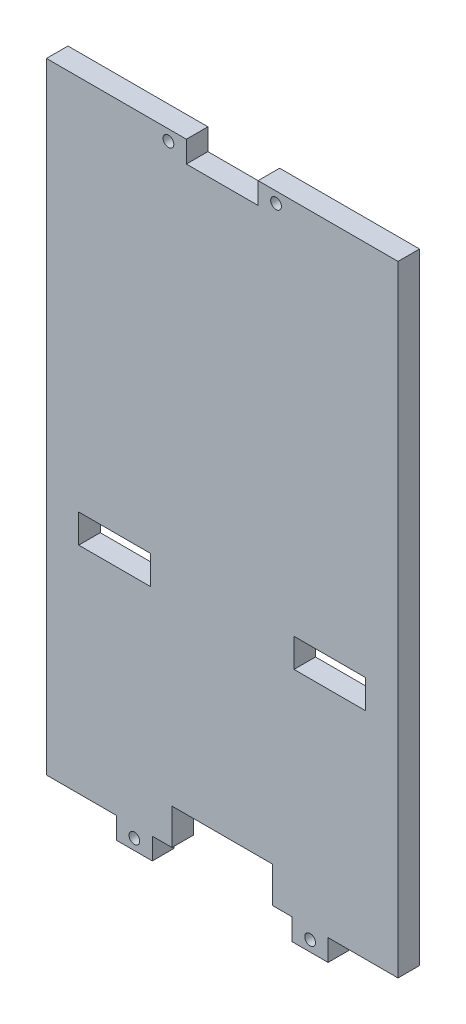
SolidWorks part; units mm, degrees
ref_plane "Plan de face" through (0, 0, 0) normal (0, 0, 1) x (1, 0, 0)
ref_plane "Plan de dessus" through (0, 0, 0) normal (0, 1, 0) x (1, 0, 0)
ref_plane "Plan de droite" through (0, 0, 0) normal (1, 0, 0) x (0, 0, -1)
sketch "Esquisse1" plane through (0, 0, 0) normal (0, 0, 1) x (1, 0, 0)
  line L0 (0, 176.8395) -> (0, -221.1538) construction
  line L1 (-49, 86.5) -> (49, 86.5)
  line L2 (-49, 86.5) -> (-49, -86.5)
  line L3 (-49, -86.5) -> (49, -86.5)
  line L4 (49, 86.5) -> (49, -86.5)
  line L5 (376.8436, 0) -> (-286.1998, 0) construction
  line L6 (-376.8436, 0) -> (286.1998, 0) construction
  line L7 (20, -18.5) -> (20, -26.5)
  line L8 (-40, -18.5) -> (-20, -18.5)
  line L9 (-40, -18.5) -> (-40, -26.5)
  line L10 (-40, -26.5) -> (-20, -26.5)
  line L11 (-20, -18.5) -> (-20, -26.5)
  line L12 (40, -26.5) -> (20, -26.5)
  line L13 (40, -18.5) -> (40, -26.5)
  line L14 (40, -18.5) -> (20, -18.5)
  dimension "D1" = 173
  dimension "D2" = 98
  dimension "D3" = 49
  dimension "D4" = 86.5
  dimension "D5" = 8
  dimension "D6" = 20
  dimension "D7" = 60
  dimension "D8" = 9
extrude "Boss.-Extru.1" add sketch "Esquisse1" along normal blind 6
sketch "Esquisse2" plane through (0, 0, 6) normal (0, 0, 1) x (1, 0, 0)
  line L1 (-49, -86.5) -> (49, -86.5) construction
  line L2 (29.5, -86.5) -> (19.5, -86.5)
  line L3 (29.5, -86.5) -> (29.5, -92.5)
  line L4 (29.5, -92.5) -> (19.5, -92.5)
  line L6 (154.6429, 0) -> (-167.6281, 0) construction
  line L7 (19.5, -86.5) -> (19.5, -92.5)
  line L8 (-49, 86.5) -> (-49, -86.5) construction
  line L9 (-19.5, -86.5) -> (-29.5, -86.5)
  line L10 (-19.5, -86.5) -> (-19.5, -92.5)
  line L11 (-19.5, -92.5) -> (-29.5, -92.5)
  line L12 (-29.5, -86.5) -> (-29.5, -92.5)
  dimension "D1" = 6
  dimension "D2" = 6
  dimension "D3" = 10
  dimension "D4" = 10
  dimension "D5" = 19.5
  dimension "D6" = 39
extrude "Boss.-Extru.2" add sketch "Esquisse2" against normal blind 6
sketch "Esquisse3" plane through (0, 0, 6) normal (0, 0, 1) x (1, 0, 0)
  line L0 (-49, 86.5) -> (-49, -86.5) construction
  line L1 (55.0284, -89.5) -> (-66.8616, -89.5) construction
  line L2 (84.5882, 83.5) -> (-34.9143, 83.5) construction
  line L3 (19.5, -92.5) -> (29.5, -92.5) construction
  line L4 (49, -86.5) -> (49, 86.5) construction
  line L5 (49, 86.5) -> (-49, 86.5) construction
  line L6 (-29.5, -86.5) -> (-29.5, -92.5) construction
  line L7 (19.5, -86.5) -> (19.5, -92.5) construction
  circle A0 centre (-15, 83.5) radius 1.5
  circle A1 centre (24.5, -89.5) radius 1.5
  circle A2 centre (-24.5, -89.5) radius 1.5
  circle A3 centre (15, 83.5) radius 1.5
  dimension "D1" = 3
  dimension "D2" = 3
  dimension "D3" = 34
  dimension "D4" = 34
  dimension "D7" = 3
  dimension "D8" = 3
  dimension "D9" = 5
  dimension "D10" = 5
  dimension "D5" = 3
  dimension "D6" = 3
extrude "Enlèv. mat.-Extru.1" cut sketch "Esquisse3" against normal blind 6
sketch "Esquisse4" plane through (0, 0, 6) normal (0, 0, 1) x (1, 0, 0)
  line L0 (49, 86.5) -> (-49, 86.5) construction
  line L1 (-10, 86.5) -> (10, 86.5)
  line L2 (-10, 86.5) -> (-10, 80.5)
  line L3 (-10, 80.5) -> (10, 80.5)
  line L4 (10, 86.5) -> (10, 80.5)
  line L5 (49, -86.5) -> (49, 86.5) construction
  line L6 (-19.5, -86.5) -> (19.5, -86.5) construction
  line L7 (-14, -86.5) -> (14, -86.5)
  line L8 (-14, -86.5) -> (-14, -76.5)
  line L9 (-14, -76.5) -> (14, -76.5)
  line L10 (14, -86.5) -> (14, -76.5)
  line L11 (-19.5, -92.5) -> (-19.5, -86.5) construction
  dimension "D1" = 6
  dimension "D2" = 20
  dimension "D3" = 39
  dimension "D4" = 10
  dimension "D5" = 28
  dimension "D6" = 5.5
extrude "Enlèv. mat.-Extru.2" cut sketch "Esquisse4" against normal blind 6
equation "\"D3@Esquisse1\"=\"D2@Esquisse1\"/2"
equation "\"D4@Esquisse1\"=\"D1@Esquisse1\"/2"
